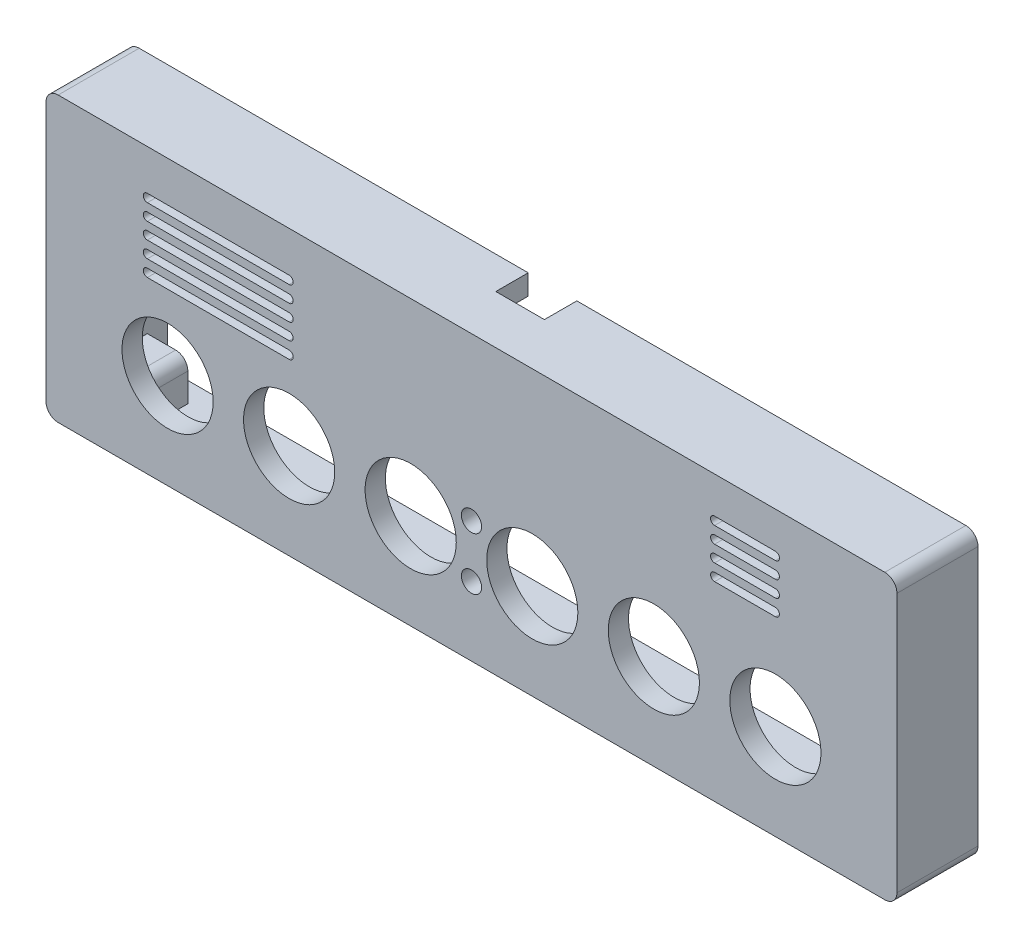
SolidWorks part; units mm, degrees
ref_plane "前视基准面" through (0, 0, 0) normal (0, 0, 1) x (1, 0, 0)
ref_plane "上视基准面" through (0, 0, 0) normal (0, 1, 0) x (1, 0, 0)
ref_plane "右视基准面" through (0, 0, 0) normal (1, 0, 0) x (0, 0, -1)
sketch "草图1" plane through (0, 0, 0) normal (0, 0, 1) x (1, 0, 0)
  line L1 (-30, 46.5) -> (180, 46.5)
  line L2 (-30, 46.5) -> (-30, -23.5)
  line L3 (-30, -23.5) -> (180, -23.5)
  line L5 (180, 46.5) -> (180, -23.5)
  dimension "D1" = 210
  dimension "D2" = 70
  dimension "D3" = 46.5
  dimension "D4" = 30
extrude "凸台-拉伸1" add sketch "草图1" along normal blind 20
fillet "圆角1" radius 3 4 edges at (180, -23.5, 10) (180, 46.5, 10) (-30, -23.5, 10) (-30, 46.5, 10)
sketch "草图2" plane through (0, 0, 0) normal (0, 0, 1) x (1, 0, 0)
  line L0 (-30, 43.5) -> (-30, -20.5) construction
  line L1 (-20, 41.5) -> (170, 41.5)
  line L2 (-20, 41.5) -> (-20, -18.5)
  line L3 (-20, -18.5) -> (170, -18.5)
  line L4 (170, 41.5) -> (170, -18.5)
  line L5 (177, 46.5) -> (-27, 46.5) construction
  line L6 (180, -20.5) -> (180, 43.5) construction
  line L7 (-27, -23.5) -> (177, -23.5) construction
  dimension "D1" = 10
  dimension "D2" = 5
  dimension "D3" = 10
  dimension "D4" = 5
extrude "切除-拉伸1" cut sketch "草图2" along normal blind 15
sketch "草图3" plane through (0, 0, 0) normal (0, 0, 1) x (1, 0, 0)
  line L0 (-30, 43.5) -> (-30, -20.5) construction
  line L4 (180, -20.5) -> (180, 43.5) construction
  line L6 (-27, -23.5) -> (177, -23.5) construction
  line L9 (177, 46.5) -> (-27, 46.5) construction
  circle A0 centre (-25, 36.5) radius 1.5
  circle A1 centre (175, 36.5) radius 1.5
  circle A2 centre (-25, -13.5) radius 1.5
  circle A3 centre (175, -13.5) radius 1.5
  dimension "D1" = 3
  dimension "D3" = 10
  dimension "D4" = 5
  dimension "D5" = 10
  dimension "D6" = 3
  dimension "D7" = 3
  dimension "D8" = 5
  dimension "D9" = 10
  dimension "D10" = 5
  dimension "D11" = 3
  dimension "D12" = 10
  dimension "D2" = 5
extrude "切除-拉伸2" cut sketch "草图3" along normal blind 8
sketch "草图4" plane through (0, 46.5, 0) normal (0, 1, 0) x (1, 0, 0)
  line L0 (75, -20) -> (75, 0) construction
  line L1 (177, -20) -> (-27, -20) construction
  line L2 (177, 0) -> (-27, 0) construction
  line L3 (177, 0) -> (-27, 0) construction
  line L4 (69, -8) -> (81, -8)
  line L5 (69, -8) -> (69, 0)
  line L6 (69, 0) -> (81, 0)
  line L7 (81, -8) -> (81, 0)
  line L8 (69, -8) -> (81, 0) construction
  line L9 (69, 0) -> (81, -8) construction
  point P6 (75, -4)
  point P13 (0, 0)
  dimension "D1" = 8
  dimension "D2" = 12
  dimension "D3" = 8
extrude "切除-拉伸3" cut sketch "草图4" against normal blind 5
sketch "草图5" plane through (0, 0, 20) normal (0, 0, 1) x (1, 0, 0)
  line L0 (0, 0) -> (150, 0) construction
  line L1 (-5, 35.5) -> (30, 35.5) construction
  line L2 (-5, 36.5) -> (30, 36.5)
  line L3 (-5, 34.5) -> (30, 34.5)
  line L4 (-5, 31.5) -> (30, 31.5) construction
  line L5 (-5, 32.5) -> (30, 32.5)
  line L6 (-5, 30.5) -> (30, 30.5)
  line L7 (-5, 27.5) -> (30, 27.5) construction
  line L8 (-5, 28.5) -> (30, 28.5)
  line L9 (-5, 26.5) -> (30, 26.5)
  line L10 (-5, 23.5) -> (30, 23.5) construction
  line L11 (-5, 24.5) -> (30, 24.5)
  line L12 (-5, 22.5) -> (30, 22.5)
  line L13 (-5, 19.5) -> (30, 19.5) construction
  line L14 (-5, 20.5) -> (30, 20.5)
  line L15 (-5, 18.5) -> (30, 18.5)
  line L17 (180, -20.5) -> (180, 43.5) construction
  line L25 (177, 46.5) -> (-27, 46.5) construction
  line L26 (-30, 43.5) -> (-30, -20.5) construction
  line L27 (135, 36.5) -> (150, 36.5) construction
  line L28 (135, 37.5) -> (150, 37.5)
  line L29 (135, 35.5) -> (150, 35.5)
  line L31 (180, -20.5) -> (180, 43.5) construction
  line L32 (135, 32.5) -> (150, 32.5) construction
  line L33 (135, 33.5) -> (150, 33.5)
  line L34 (135, 31.5) -> (150, 31.5)
  line L35 (135, 28.5) -> (150, 28.5) construction
  line L36 (135, 29.5) -> (150, 29.5)
  line L37 (135, 27.5) -> (150, 27.5)
  line L38 (135, 24.5) -> (150, 24.5) construction
  line L39 (135, 25.5) -> (150, 25.5)
  line L40 (135, 23.5) -> (150, 23.5)
  line L493 (-5, 15.5) -> (30, 15.5) construction
  line L494 (-5, 16.5) -> (30, 16.5) [skipped]
  line L495 (-5, 14.5) -> (30, 14.5) [skipped]
  line L496 (-5, 11.5) -> (30, 11.5) construction
  line L497 (-5, 12.5) -> (30, 12.5) [skipped]
  line L498 (-5, 10.5) -> (30, 10.5) [skipped]
  line L499 (-5, 7.5) -> (30, 7.5) construction
  line L500 (-5, 8.5) -> (30, 8.5) [skipped]
  line L501 (-5, 6.5) -> (30, 6.5) [skipped]
  line L502 (-5, 15.5) -> (30, 15.5) construction
  line L503 (-5, 16.5) -> (30, 16.5) [skipped]
  line L504 (-5, 14.5) -> (30, 14.5) [skipped]
  line L505 (-5, 11.5) -> (30, 11.5) construction
  line L506 (-5, 12.5) -> (30, 12.5) [skipped]
  line L507 (-5, 10.5) -> (30, 10.5) [skipped]
  line L508 (-5, 7.5) -> (30, 7.5) construction
  line L509 (-5, 8.5) -> (30, 8.5) [skipped]
  line L510 (-5, 6.5) -> (30, 6.5) [skipped]
  circle A0 centre (0, 0) radius 11.25
  circle A1 centre (30, 0) radius 11.25
  circle A2 centre (60, 0) radius 11.25
  circle A3 centre (90, 0) radius 11.25
  circle A4 centre (120, 0) radius 11.25
  circle A5 centre (150, 0) radius 11.25
  circle A6 centre (75, -6.5) radius 2.5
  circle A7 centre (75, 6.5) radius 2.5
  arc A8 (-5, 36.5) -> (-5, 34.5) centre (-5, 35.5) ccw
  arc A9 (30, 34.5) -> (30, 36.5) centre (30, 35.5) ccw
  arc A10 (-5, 32.5) -> (-5, 30.5) centre (-5, 31.5) ccw
  arc A11 (30, 30.5) -> (30, 32.5) centre (30, 31.5) ccw
  arc A12 (-5, 28.5) -> (-5, 26.5) centre (-5, 27.5) ccw
  arc A13 (30, 26.5) -> (30, 28.5) centre (30, 27.5) ccw
  arc A14 (-5, 24.5) -> (-5, 22.5) centre (-5, 23.5) ccw
  arc A15 (30, 22.5) -> (30, 24.5) centre (30, 23.5) ccw
  arc A16 (-5, 20.5) -> (-5, 18.5) centre (-5, 19.5) ccw
  arc A17 (30, 18.5) -> (30, 20.5) centre (30, 19.5) ccw
  arc A24 (135, 37.5) -> (135, 35.5) centre (135, 36.5) ccw
  arc A25 (150, 35.5) -> (150, 37.5) centre (150, 36.5) ccw
  arc A26 (135, 33.5) -> (135, 31.5) centre (135, 32.5) ccw
  arc A27 (150, 31.5) -> (150, 33.5) centre (150, 32.5) ccw
  arc A28 (135, 29.5) -> (135, 27.5) centre (135, 28.5) ccw
  arc A29 (150, 27.5) -> (150, 29.5) centre (150, 28.5) ccw
  arc A30 (135, 25.5) -> (135, 23.5) centre (135, 24.5) ccw
  arc A31 (150, 23.5) -> (150, 25.5) centre (150, 24.5) ccw
  arc A340 (-5, 16.5) -> (-5, 14.5) centre (-5, 15.5) ccw [skipped]
  arc A341 (30, 14.5) -> (30, 16.5) centre (30, 15.5) ccw [skipped]
  arc A342 (-5, 12.5) -> (-5, 10.5) centre (-5, 11.5) ccw [skipped]
  arc A343 (30, 10.5) -> (30, 12.5) centre (30, 11.5) ccw [skipped]
  arc A344 (-5, 8.5) -> (-5, 6.5) centre (-5, 7.5) ccw [skipped]
  arc A345 (30, 6.5) -> (30, 8.5) centre (30, 7.5) ccw [skipped]
  point P16 (75, 0)
  point P20 (12.5, 35.5)
  point P29 (12.5, 31.5)
  point P36 (12.5, 27.5)
  point P43 (12.5, 23.5)
  point P50 (12.5, 19.5)
  point P64 (12.5, 20.5)
  point P71 (12.5, 17.5)
  point P80 (142.5, 36.5)
  point P91 (142.5, 32.5)
  point P98 (142.5, 28.5)
  point P105 (142.5, 24.5)
  point P110 (12.5, 14.5)
  point P117 (12.5, 20.5)
  point P124 (12.5, 17.5)
  point P131 (12.5, 14.5)
  point P138 (12.5, 20.5)
  point P145 (12.5, 17.5)
  point P152 (12.5, 14.5)
  point P159 (12.5, 20.5)
  point P166 (12.5, 17.5)
  point P173 (12.5, 14.5)
  point P180 (12.5, 20.5)
  point P187 (12.5, 17.5)
  point P194 (12.5, 14.5)
  point P201 (12.5, 20.5)
  point P208 (12.5, 17.5)
  point P215 (12.5, 14.5)
  point P222 (12.5, 15.5)
  point P229 (12.5, 11.5)
  point P236 (12.5, 7.5)
  point P243 (12.5, 15.5)
  point P250 (12.5, 11.5)
  point P257 (12.5, 7.5)
  point P264 (12.5, 15.5)
  point P271 (12.5, 11.5)
  point P278 (12.5, 7.5)
  point P285 (12.5, 15.5)
  point P292 (12.5, 11.5)
  point P299 (12.5, 7.5)
  point P306 (12.5, 15.5)
  point P313 (12.5, 11.5)
  point P320 (12.5, 7.5)
  point P327 (12.5, 15.5)
  point P334 (12.5, 11.5)
  point P341 (12.5, 7.5)
  point P348 (12.5, 15.5)
  point P355 (12.5, 11.5)
  point P362 (12.5, 7.5)
  point P369 (12.5, 15.5)
  point P376 (12.5, 11.5)
  point P383 (12.5, 7.5)
  point P390 (12.5, 15.5)
  point P397 (12.5, 11.5)
  point P404 (12.5, 7.5)
  point P411 (12.5, 15.5)
  point P418 (12.5, 11.5)
  point P425 (12.5, 7.5)
  point P432 (12.5, 15.5)
  point P439 (12.5, 11.5)
  point P446 (12.5, 7.5)
  point P453 (12.5, 15.5)
  point P460 (12.5, 11.5)
  point P467 (12.5, 7.5)
  point P474 (12.5, 15.5)
  point P481 (12.5, 11.5)
  point P488 (12.5, 7.5)
  point P495 (12.5, 15.5)
  point P502 (12.5, 11.5)
  point P509 (12.5, 7.5)
  point P516 (12.5, 15.5)
  point P523 (12.5, 11.5)
  point P530 (12.5, 7.5)
  point P537 (12.5, 15.5)
  point P544 (12.5, 11.5)
  point P551 (12.5, 7.5)
  point P558 (12.5, 15.5)
  point P565 (12.5, 11.5)
  point P572 (12.5, 7.5)
  point P579 (12.5, 15.5)
  point P586 (12.5, 11.5)
  point P593 (12.5, 7.5)
  point P600 (12.5, 15.5)
  point P607 (12.5, 11.5)
  point P614 (12.5, 7.5)
  point P621 (12.5, 15.5)
  point P628 (12.5, 11.5)
  point P635 (12.5, 7.5)
  point P642 (12.5, 15.5)
  point P649 (12.5, 11.5)
  point P656 (12.5, 7.5)
  point P663 (12.5, 15.5)
  point P670 (12.5, 11.5)
  point P677 (12.5, 7.5)
  point P684 (12.5, 15.5)
  point P691 (12.5, 11.5)
  point P698 (12.5, 7.5)
  point P705 (12.5, 15.5)
  point P712 (12.5, 11.5)
  point P719 (12.5, 7.5)
  point P726 (12.5, 15.5)
  point P733 (12.5, 11.5)
  point P740 (12.5, 7.5)
  point P747 (12.5, 15.5)
  point P754 (12.5, 11.5)
  point P761 (12.5, 7.5)
  point P768 (12.5, 15.5)
  point P775 (12.5, 11.5)
  point P782 (12.5, 7.5)
  point P789 (12.5, 15.5)
  point P796 (12.5, 11.5)
  point P803 (12.5, 7.5)
  point P810 (12.5, 15.5)
  point P817 (12.5, 11.5)
  point P824 (12.5, 7.5)
  point P831 (12.5, 15.5)
  point P838 (12.5, 11.5)
  point P845 (12.5, 7.5)
  point P852 (12.5, 15.5)
  point P859 (12.5, 11.5)
  point P866 (12.5, 7.5)
  point P873 (12.5, 15.5)
  point P880 (12.5, 11.5)
  point P887 (12.5, 7.5)
  point P894 (12.5, 15.5)
  point P901 (12.5, 11.5)
  point P908 (12.5, 7.5)
  point P915 (12.5, 15.5)
  point P922 (12.5, 11.5)
  point P929 (12.5, 7.5)
  point P936 (12.5, 15.5)
  point P943 (12.5, 11.5)
  point P950 (12.5, 7.5)
  point P957 (12.5, 15.5)
  point P964 (12.5, 11.5)
  point P971 (12.5, 7.5)
  point P978 (12.5, 15.5)
  point P985 (12.5, 11.5)
  point P992 (12.5, 7.5)
  point P999 (12.5, 15.5)
  point P1006 (12.5, 11.5)
  point P1013 (12.5, 7.5)
  point P1020 (12.5, 15.5)
  point P1027 (12.5, 11.5)
  point P1034 (12.5, 7.5)
  point P1041 (12.5, 15.5)
  point P1048 (12.5, 11.5)
  point P1055 (12.5, 7.5)
  point P1062 (12.5, 15.5)
  point P1069 (12.5, 11.5)
  point P1076 (12.5, 7.5)
  point P1083 (12.5, 15.5)
  point P1090 (12.5, 11.5)
  point P1097 (12.5, 7.5)
  point P1104 (12.5, 15.5)
  point P1111 (12.5, 11.5)
  point P1118 (12.5, 7.5)
  point P1125 (12.5, 15.5)
  point P1132 (12.5, 11.5)
  point P1139 (12.5, 7.5)
  point P1146 (12.5, 15.5)
  point P1153 (12.5, 11.5)
  point P1160 (12.5, 7.5)
  point P1167 (12.5, 15.5)
  point P1174 (12.5, 11.5)
  point P1181 (12.5, 7.5)
  point P1188 (12.5, 15.5)
  point P1195 (12.5, 11.5)
  point P1202 (12.5, 7.5)
  dimension "D1" = 22.5
  dimension "D2" = 6
  dimension "D5" = 5
  dimension "D6" = 35
  dimension "D12" = 25
  dimension "D16" = 30
  dimension "D19" = 30
  dimension "D3" = 30
  dimension "D4" = 6.5
  dimension "D7" = 2
  dimension "D9" = 10
  dimension "D10" = 25
  dimension "D11" = 2
  dimension "D13" = 15
  dimension "D14" = 2
  dimension "D15" = 10
  dimension "D17" = 4
  dimension "D18" = 2
  dimension "D8" = 8
extrude "切除-拉伸4" cut sketch "草图5" against normal blind 10
sketch "草图6" plane through (0, 0, 15) normal (0, 0, 1) x (1, 0, 0)
  line L0 (75, 46.5) -> (75, -23.5) construction
  line L1 (177, 46.5) -> (-27, 46.5) construction
  line L2 (-27, -23.5) -> (177, -23.5) construction
  line L4 (-30, 11.5) -> (180, 11.5) construction
  line L5 (-30, 43.5) -> (-30, -20.5) construction
  line L6 (180, -20.5) -> (180, 43.5) construction
  line L7 (-20, 31.5) -> (-13, 31.5)
  line L8 (-20, 41.5) -> (-10, 41.5)
  line L9 (-20, 41.5) -> (-20, 31.5)
  line L10 (170, 41.5) -> (170, 31.5)
  line L11 (170, 31.5) -> (163, 31.5)
  line L12 (-10, 34.5) -> (-10, 41.5)
  line L13 (160, 34.5) -> (160, 41.5)
  line L14 (170, 41.5) -> (160, 41.5)
  line L15 (-20, -8.5) -> (-13, -8.5)
  line L16 (-10, -11.5) -> (-10, -18.5)
  line L17 (-20, -18.5) -> (-20, -8.5)
  line L18 (-20, -18.5) -> (-10, -18.5)
  line L19 (170, -18.5) -> (160, -18.5)
  line L20 (160, -11.5) -> (160, -18.5)
  line L21 (170, -18.5) -> (170, -8.5)
  line L22 (170, -8.5) -> (163, -8.5)
  arc A5 (-13, 31.5) -> (-10, 34.5) centre (-13, 34.5) ccw
  arc A6 (163, 31.5) -> (160, 34.5) centre (163, 34.5) cw
  arc A7 (-13, -8.5) -> (-10, -11.5) centre (-13, -11.5) cw
  arc A8 (163, -8.5) -> (160, -11.5) centre (163, -11.5) ccw
  point P37 (-10, 31.5)
  dimension "D5" = 3
  dimension "D4" = 5
  dimension "D6" = 10
  dimension "D8" = 10
  dimension "D9" = 10
extrude "凸台-拉伸2" add sketch "草图6" against normal blind 10
sketch "草图8" plane through (0, 0, 5) normal (0, 0, -1) x (-1, 0, 0)
  line L0 (-170, 41.5) -> (-160, 41.5) construction
  line L1 (-170, 31.5) -> (-170, 41.5) construction
  line L2 (-160, 38) -> (10, 38) construction
  line L3 (-160, 41.5) -> (-160, 34.5) construction
  line L4 (10, 34.5) -> (10, 41.5) construction
  line L8 (-75, 38) -> (-75, -15) construction
  line L9 (-166.5, 31.5) -> (-166.5, -8.5) construction
  line L12 (-163, 31.5) -> (-170, 31.5) construction
  line L13 (-170, -8.5) -> (-163, -8.5) construction
  line L14 (16.5, 31.5) -> (16.5, -8.5) construction
  line L15 (20, 31.5) -> (13, 31.5) construction
  line L16 (13, -8.5) -> (20, -8.5) construction
  line L17 (-166.5, 11.5) -> (16.5, 11.5) construction
  circle A0 centre (-165, 36.5) radius 1.5
  circle A1 centre (15, 36.5) radius 1.5
  circle A2 centre (-165, -13.5) radius 1.5
  circle A3 centre (15, -13.5) radius 1.5
  dimension "D1" = 3
  dimension "D2" = 5
  dimension "D3" = 5
extrude "切除-拉伸5" cut sketch "草图8" against normal blind 8
